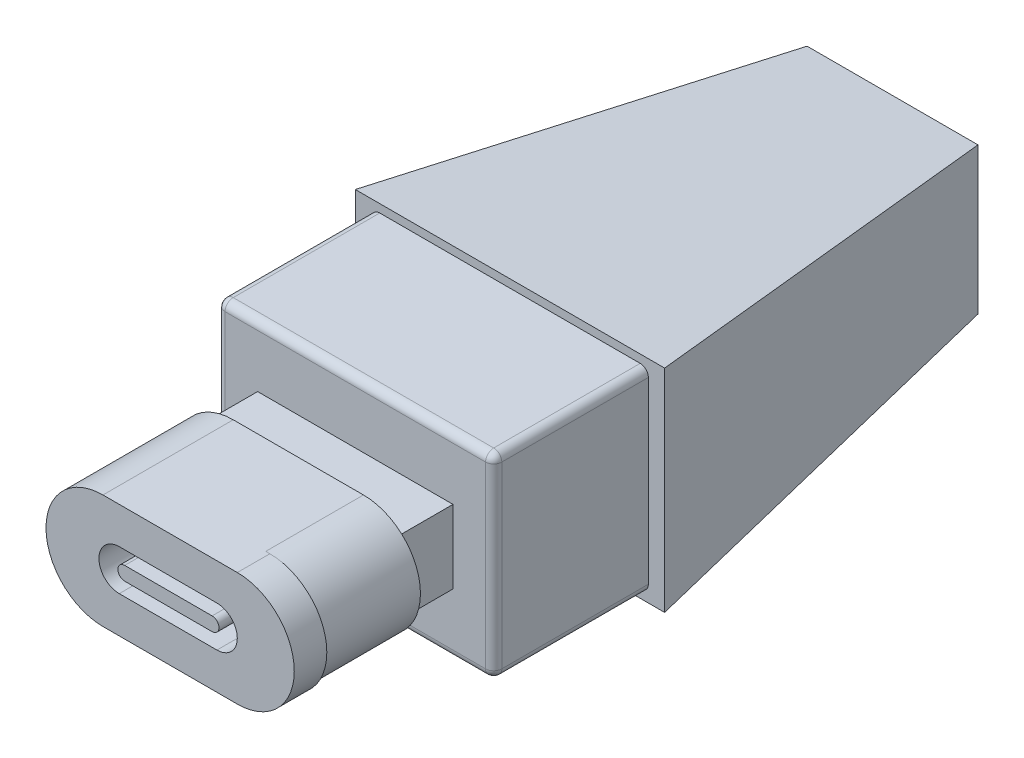
SolidWorks part; units mm, degrees
ref_plane "Alzado" through (0, 0, 0) normal (0, 0, 1) x (1, 0, 0)
ref_plane "Planta" through (0, 0, 0) normal (0, 1, 0) x (1, 0, 0)
ref_plane "Vista lateral" through (0, 0, 0) normal (1, 0, 0) x (0, 0, -1)
sketch "Croquis1" plane through (0, 0, 0) normal (0, 0, 1) x (1, 0, 0)
  line L0 (-4, 0) -> (4, 0) construction
  line L1 (-4, 3.5) -> (4, 3.5)
  line L2 (-4, -3.5) -> (4, -3.5)
  arc A0 (-4, 3.5) -> (-4, -3.5) centre (-4, 0) ccw
  arc A1 (4, -3.5) -> (4, 3.5) centre (4, 0) ccw
  point P3 (0, 0)
  point P8 (-9.2957, -3.5)
  point P9 (0, 0)
  point P10 (-7.5, 0)
  point P11 (7.5, 0)
  dimension "D1" = 7
  dimension "D2" = 8
extrude "Saliente-Extruir1" add sketch "Croquis1" along normal blind 6
sketch "Croquis2" plane through (0, 0, 6) normal (0, 0, 1) x (1, 0, 0)
  line L0 (-4, 0) -> (4.25, 0) construction
  line L1 (-4, 3.5) -> (4.25, 3.5)
  line L2 (-4, -3.5) -> (4.25, -3.5)
  line L3 (7.5, 0) -> (7.75, 0) construction
  arc A0 (-4, 3.5) -> (-4, -3.5) centre (-4, 0) ccw
  arc A1 (4.25, -3.5) -> (4.25, 3.5) centre (4.25, 0) ccw
  arc A2 (4, -3.5) -> (4, 3.5) centre (4, 0) ccw construction
  point P4 (0.125, 0)
  dimension "D1" = 7
  dimension "D2" = 0.25
extrude "Saliente-Extruir2" add sketch "Croquis2" along normal blind 2
sketch "Croquis3" plane through (0, 0, 0) normal (0, 0, -1) x (-1, 0, 0)
  line L1 (-6, -2.25) -> (6, -2.25)
  line L2 (-6, -2.25) -> (-6, 2.25)
  line L3 (-6, 2.25) -> (6, 2.25)
  line L4 (6, -2.25) -> (6, 2.25)
  line L5 (-6, -2.25) -> (6, 2.25) construction
  line L6 (-6, 2.25) -> (6, -2.25) construction
  point P0 (0, 0)
  dimension "D1" = 12
  dimension "D2" = 4.5
extrude "Saliente-Extruir3" add sketch "Croquis3" along normal blind 3.5
sketch "Croquis4" plane through (0, 0, -3.5) normal (0, 0, -1) x (-1, 0, 0)
  line L1 (-8.5, -6) -> (8.5, -6)
  line L2 (-8.5, -6) -> (-8.5, 6)
  line L3 (-8.5, 6) -> (8.5, 6)
  line L4 (8.5, -6) -> (8.5, 6)
  line L5 (-8.5, -6) -> (8.5, 6) construction
  line L6 (-8.5, 6) -> (8.5, -6) construction
  point P0 (0, 0)
  dimension "D1" = 17
  dimension "D2" = 12
extrude "Saliente-Extruir4" add sketch "Croquis4" along normal blind 9.5
sketch "Croquis5" plane through (0, 0, -13) normal (0, 0, -1) x (-1, 0, 0)
  line L1 (-9.5, -6.5) -> (9.5, -6.5)
  line L2 (-9.5, -6.5) -> (-9.5, 6.5)
  line L3 (-9.5, 6.5) -> (9.5, 6.5)
  line L4 (9.5, -6.5) -> (9.5, 6.5)
  line L5 (-9.5, -6.5) -> (9.5, 6.5) construction
  line L6 (-9.5, 6.5) -> (9.5, -6.5) construction
  point P0 (0, 0)
  dimension "D1" = 13
  dimension "D2" = 19
ref_plane "Plano1" through (0, 0, -36.5) normal (0, 0, -1) x (-1, 0, 0)
sketch "Croquis6" plane through (0, 0, -36.5) normal (0, 0, -1) x (-1, 0, 0)
  line L1 (-5.25, -4.5) -> (5.25, -4.5)
  line L2 (-5.25, -4.5) -> (-5.25, 4.5)
  line L3 (-5.25, 4.5) -> (5.25, 4.5)
  line L4 (5.25, -4.5) -> (5.25, 4.5)
  line L5 (-5.25, -4.5) -> (5.25, 4.5) construction
  line L6 (-5.25, 4.5) -> (5.25, -4.5) construction
  point P0 (0, 0)
  dimension "D1" = 10.5
  dimension "D2" = 9
loft "Recubrir1" add profiles "Croquis5", "Croquis6"
fillet "Redondeo1" radius 0.5 8 edges at (0, -6, -3.5) (-8.5, 0, -3.5) (0, 6, -3.5) (8.5, 0, -3.5) (-8.5, -6, -8.25) (8.5, -6, -8.25) (-8.5, 6, -8.25) (8.5, 6, -8.25)
sketch "Croquis7" plane through (0, 0, 8) normal (0, 0, 1) x (1, 0, 0)
  line L0 (-3, 0) -> (3, 0) construction
  line L1 (-3, 1.25) -> (3, 1.25)
  line L2 (-3, -1.25) -> (3, -1.25)
  line L4 (-6, -2.25) -> (-6, 2.25) construction
  arc A0 (-3, 1.25) -> (-3, -1.25) centre (-3, 0) ccw
  arc A1 (3, -1.25) -> (3, 1.25) centre (3, 0) ccw
  point P4 (0, 0)
  point P9 (-4.25, 0)
  point P10 (4.25, 0)
  point P11 (-3.0661, 0)
  dimension "D1" = 2.5
  dimension "D2" = 8.5
  dimension "D3" = 6
extrude "Cortar-Extruir1" cut sketch "Croquis7" against normal blind 3
sketch "Croquis8" plane through (0, 0, 5) normal (0, 0, 1) x (1, 0, 0)
  line L0 (-2.6656, 0) -> (2.7047, 0) construction
  line L1 (-2.6656, 0.4199) -> (2.7047, 0.4199)
  line L2 (-2.6656, -0.4199) -> (2.7047, -0.4199)
  arc A0 (-2.6656, 0.4199) -> (-2.6656, -0.4199) centre (-2.6656, 0) ccw
  arc A1 (2.7047, -0.4199) -> (2.7047, 0.4199) centre (2.7047, 0) ccw
  point P3 (0.0195, 0)
extrude "Saliente-Extruir5" add sketch "Croquis8" along normal blind 3
